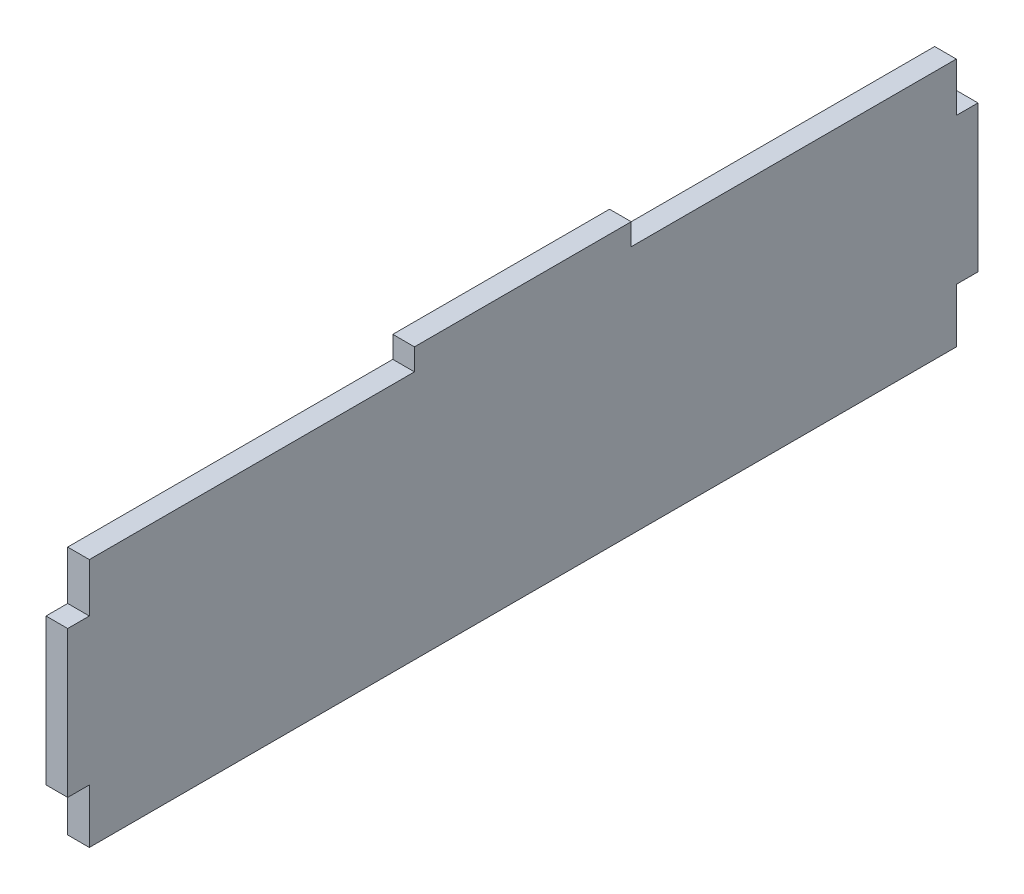
SolidWorks part; units mm, degrees
ref_plane "Front Plane" through (0, 0, 0) normal (0, 0, 1) x (1, 0, 0)
ref_plane "Top Plane" through (0, 0, 0) normal (0, 1, 0) x (1, 0, 0)
ref_plane "Right Plane" through (0, 0, 0) normal (1, 0, 0) x (0, 0, -1)
sketch "Sketch2" plane through (0, 0, 0) normal (1, 0, 0) x (0, 0, -1)
  line L1 (61, 3.0154) -> (101, 3.0154)
  line L3 (1, -47) -> (161, -47)
  line L5 (-3, -10) -> (-3, -37)
  line L10 (1, -0.9846) -> (61, -0.9846)
  line L11 (61, 3.0154) -> (61, -0.9846)
  line L12 (101, 3.0154) -> (101, -0.9846)
  line L13 (165, -10) -> (165, -37)
  line L14 (101, -0.9846) -> (161, -0.9846)
  line L16 (1, -0.9846) -> (1, -10)
  line L17 (-3, -10) -> (1, -10)
  line L18 (-3, -37) -> (1, -37)
  line L19 (1, -37) -> (1, -47)
  line L20 (161, -0.9846) -> (161, -10)
  line L21 (165, -10) -> (161, -10)
  line L22 (165, -37) -> (161, -37)
  line L23 (161, -37) -> (161, -47)
  dimension "D1" = 4
  dimension "D2" = 27
  dimension "D3" = 4
  dimension "D4" = 4
  dimension "D6" = 40
  dimension "D8" = 50.0154
  dimension "D9" = 168
extrude "Boss-Extrude1" add sketch "Sketch2" along normal blind 4
